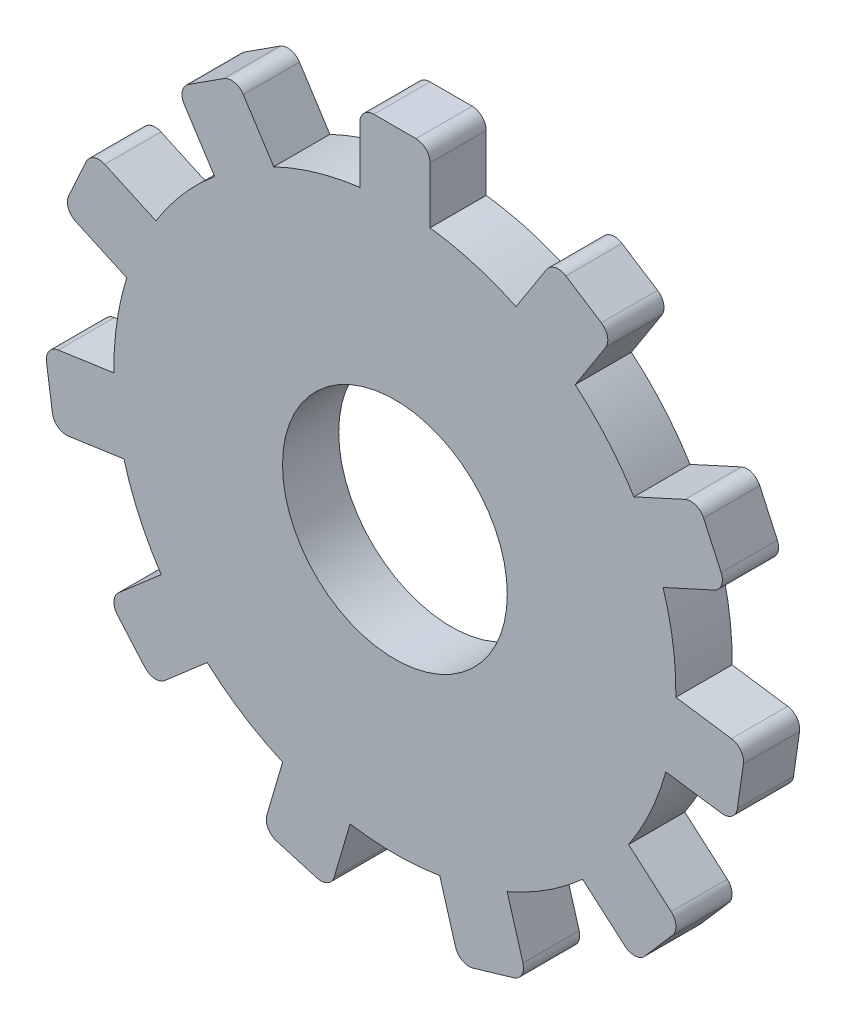
SolidWorks part; units mm, degrees
ref_plane "Front Plane" through (0, 0, 0) normal (0, 0, 1) x (1, 0, 0)
ref_plane "Top Plane" through (0, 0, 0) normal (0, 1, 0) x (1, 0, 0)
ref_plane "Right Plane" through (0, 0, 0) normal (1, 0, 0) x (0, 0, -1)
sketch "Sketch1" plane through (0, 0, 0) normal (0, 0, 1) x (1, 0, 0)
  line L0 (37.322, 51.0233) -> (30.9083, 55.1451)
  line L1 (38.0855, 47.5133) -> (32.5926, 38.9662)
  line L2 (27.3983, 54.3815) -> (21.9054, 45.8344)
  line L3 (58.9825, 22.7458) -> (55.8154, 29.6807)
  line L4 (57.7272, 19.3801) -> (48.4853, 15.1595)
  line L5 (3.8119, 63.1013) -> (-3.8119, 63.1013)
  line L6 (6.3519, 60.5613) -> (6.3519, 50.4013)
  line L8 (-6.3519, 60.5613) -> (-6.3519, 50.4013)
  line L9 (52.4498, 30.936) -> (43.208, 26.7154)
  line L10 (61.9165, -12.7534) -> (63.0015, -5.2071)
  line L11 (59.0409, -14.9061) -> (48.9843, -13.4602)
  line L12 (60.8489, -2.3315) -> (50.7923, -0.8856)
  line L13 (45.1925, -44.2035) -> (50.1851, -38.4417)
  line L14 (41.6095, -44.4597) -> (33.9311, -37.8063)
  line L15 (49.9288, -34.8587) -> (42.2504, -28.2054)
  line L16 (14.1202, -61.6192) -> (21.4352, -59.4713)
  line L17 (10.9674, -59.8977) -> (8.105, -50.1493)
  line L18 (23.1567, -56.3186) -> (20.2943, -46.5702)
  line L19 (-21.4352, -59.4713) -> (-14.1202, -61.6192)
  line L20 (-23.1567, -56.3186) -> (-20.2943, -46.5702)
  line L21 (-10.9674, -59.8977) -> (-8.105, -50.1493)
  line L22 (-50.1851, -38.4417) -> (-45.1925, -44.2035)
  line L23 (-49.9288, -34.8587) -> (-42.2504, -28.2054)
  line L24 (-41.6095, -44.4597) -> (-33.9311, -37.8063)
  line L25 (-63.0015, -5.2071) -> (-61.9165, -12.7534)
  line L26 (-60.8489, -2.3315) -> (-50.7923, -0.8856)
  line L27 (-59.0409, -14.9061) -> (-48.9843, -13.4602)
  line L28 (-55.8154, 29.6807) -> (-58.9825, 22.7458)
  line L29 (-52.4498, 30.936) -> (-43.208, 26.7154)
  line L30 (-57.7272, 19.3801) -> (-48.4853, 15.1595)
  line L31 (-30.9083, 55.1451) -> (-37.322, 51.0233)
  line L32 (-27.3983, 54.3815) -> (-21.9054, 45.8344)
  line L33 (-38.0855, 47.5133) -> (-32.5926, 38.9662)
  arc A0 (-6.3519, 50.4013) -> (-21.9054, 45.8344) centre (0, 0) ccw
  arc A1 (-3.8119, 63.1013) -> (-6.3519, 60.5613) centre (-3.8119, 60.5613) ccw
  arc A2 (3.8119, 63.1013) -> (6.3519, 60.5613) centre (3.8119, 60.5613) cw
  arc A3 (30.9083, 55.1451) -> (27.3983, 54.3815) centre (29.5351, 53.0083) ccw
  arc A4 (37.322, 51.0233) -> (38.0855, 47.5133) centre (35.9487, 48.8865) cw
  arc A5 (55.8154, 29.6807) -> (52.4498, 30.936) centre (53.505, 28.6256) ccw
  arc A6 (58.9825, 22.7458) -> (57.7272, 19.3801) centre (56.6721, 21.6906) cw
  arc A7 (63.0015, -5.2071) -> (60.8489, -2.3315) centre (60.4874, -4.8456) ccw
  arc A8 (61.9165, -12.7534) -> (59.0409, -14.9061) centre (59.4024, -12.3919) cw
  arc A9 (50.1851, -38.4417) -> (49.9288, -34.8587) centre (48.2655, -36.7783) ccw
  arc A10 (45.1925, -44.2035) -> (41.6095, -44.4597) centre (43.2729, -42.5401) cw
  arc A11 (21.4352, -59.4713) -> (23.1567, -56.3186) centre (20.7196, -57.0342) ccw
  arc A12 (14.1202, -61.6192) -> (10.9674, -59.8977) centre (13.4046, -59.1821) cw
  arc A13 (-14.1202, -61.6192) -> (-10.9674, -59.8977) centre (-13.4046, -59.1821) ccw
  arc A14 (-21.4352, -59.4713) -> (-23.1567, -56.3186) centre (-20.7196, -57.0342) cw
  arc A15 (-45.1925, -44.2035) -> (-41.6095, -44.4597) centre (-43.2729, -42.5401) ccw
  arc A16 (-50.1851, -38.4417) -> (-49.9288, -34.8587) centre (-48.2655, -36.7783) cw
  arc A17 (-61.9165, -12.7534) -> (-59.0409, -14.9061) centre (-59.4024, -12.3919) ccw
  arc A18 (-63.0015, -5.2071) -> (-60.8489, -2.3315) centre (-60.4874, -4.8456) cw
  arc A19 (-58.9825, 22.7458) -> (-57.7272, 19.3801) centre (-56.6721, 21.6906) ccw
  arc A20 (-55.8154, 29.6807) -> (-52.4498, 30.936) centre (-53.505, 28.6256) cw
  arc A21 (-37.322, 51.0233) -> (-38.0855, 47.5133) centre (-35.9487, 48.8865) ccw
  arc A22 (-30.9083, 55.1451) -> (-27.3983, 54.3815) centre (-29.5351, 53.0083) cw
  arc A23 (21.9054, 45.8344) -> (6.3519, 50.4013) centre (0, 0) ccw
  arc A24 (43.208, 26.7154) -> (32.5926, 38.9662) centre (0, 0) ccw
  arc A25 (50.7923, -0.8856) -> (48.4853, 15.1595) centre (0, 0) ccw
  arc A26 (42.2504, -28.2054) -> (48.9843, -13.4602) centre (0, 0) ccw
  arc A27 (20.2943, -46.5702) -> (33.9311, -37.8063) centre (0, 0) ccw
  arc A28 (-8.105, -50.1493) -> (8.105, -50.1493) centre (0, 0) ccw
  arc A29 (-33.9311, -37.8063) -> (-20.2943, -46.5702) centre (0, 0) ccw
  arc A30 (-48.9843, -13.4602) -> (-42.2504, -28.2054) centre (0, 0) ccw
  arc A31 (-48.4853, 15.1595) -> (-50.7923, -0.8856) centre (0, 0) ccw
  arc A32 (-32.5926, 38.9662) -> (-43.208, 26.7154) centre (0, 0) ccw
  circle A33 centre (0, 0) radius 20.32
  point P93 (0, 0)
  dimension "D1" = 2.54
  dimension "D2" = 11
extrude "Boss-Extrude3" add sketch "Sketch1" along normal blind 10.16
